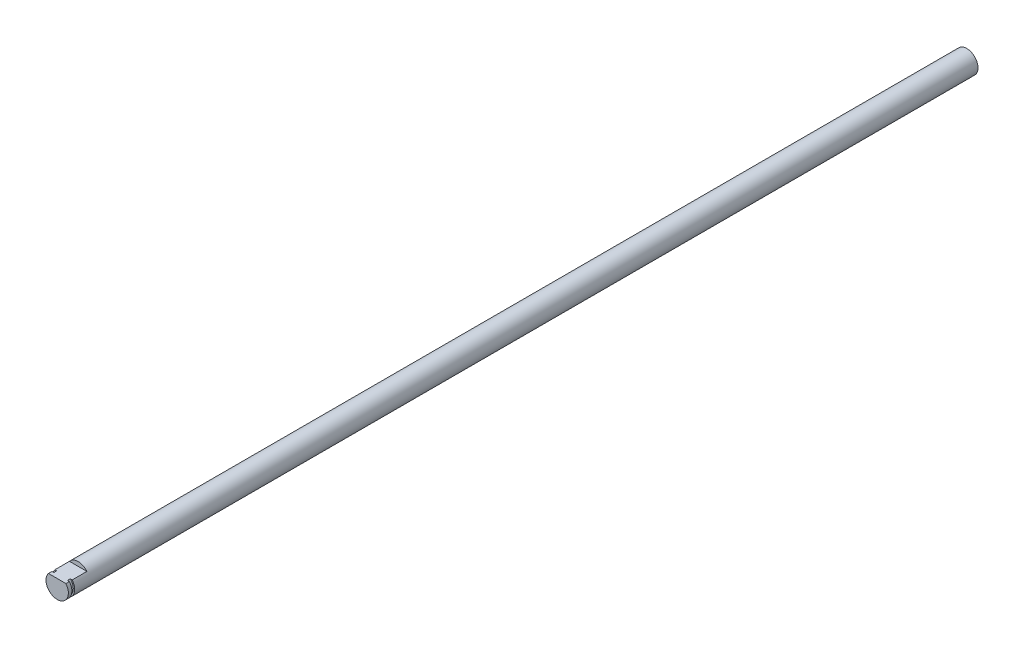
SolidWorks part; units mm, degrees
ref_plane "Front Plane" through (0, 0, 0) normal (0, 0, 1) x (1, 0, 0)
ref_plane "Top Plane" through (0, 0, 0) normal (0, 1, 0) x (1, 0, 0)
ref_plane "Right Plane" through (0, 0, 0) normal (1, 0, 0) x (0, 0, -1)
sketch "Sketch1" plane through (0, 0, 0) normal (0, 0, 1) x (1, 0, 0)
  circle A0 centre (0, 0) radius 4
  dimension "D1" = 8
extrude "Boss-Extrude1" add sketch "Sketch1" along normal blind 325
sketch "Sketch2" plane through (0, 0, 325) normal (0, 0, 1) x (1, 0, 0)
  line L0 (3.1225, 2.5) -> (-3.1225, 2.5)
  circle A1 centre (0, 0) radius 4
  arc A2 (3.1225, 2.5) -> (-3.1225, 2.5) centre (0, 0) ccw
  dimension "D2" = 2.5
  dimension "D1" = 0
extrude "Cut-Extrude1" cut sketch "Sketch2" against normal blind 7.5
ref_plane "Plane1" through (0, 0, 323.75) normal (0, 0, 1) x (1, 0, 0)
sketch "Sketch3" plane through (0, 0, 323.75) normal (0, 0, 1) x (1, 0, 0)
  circle A0 centre (0, 0) radius 4
  circle A1 centre (0, 0) radius 3.5
extrude "Cut-Extrude2" cut sketch "Sketch3" against normal blind 1
